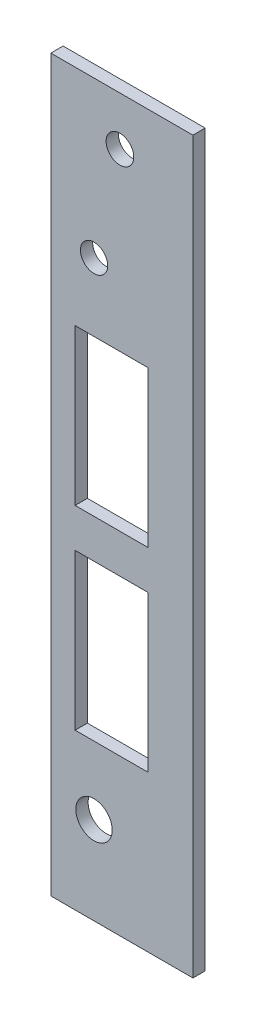
SolidWorks part; units mm, degrees
ref_plane "Front" through (0, 0, 0) normal (0, 0, 1) x (1, 0, 0)
ref_plane "Top" through (0, 0, 0) normal (0, 1, 0) x (1, 0, 0)
ref_plane "Right" through (0, 0, 0) normal (1, 0, 0) x (0, 0, -1)
sketch "Sketch1" plane through (0, 0, 0) normal (0, 0, 1) x (1, 0, 0)
  line L1 (0, 0) -> (18.542, 0)
  line L2 (0, 0) -> (0, -95.25)
  line L3 (0, -95.25) -> (18.542, -95.25)
  line L4 (18.542, 0) -> (18.542, -95.25)
  dimension "D1" = 18.542
  dimension "D2" = 95.25
extrude "Extrude1" add sketch "Sketch1" along normal blind 1.6002
sketch "Sketch2" plane through (0, 0, 1.6002) normal (0, 0, 1) x (1, 0, 0)
  line L0 (18.542, -95.25) -> (18.542, 0) construction
  line L1 (18.542, 0) -> (0, 0) construction
  circle A0 centre (9.017, -6.35) radius 1.8034
  dimension "D1" = 3.6068
  dimension "D3" = 9.525
  dimension "D4" = 6.35
extrude "Cut-Extrude1" cut sketch "Sketch2" against normal blind 1.6002
sketch "Sketch3" plane through (0, 0, 1.6002) normal (0, 0, 1) x (1, 0, 0)
  line L0 (0, -95.25) -> (18.542, -95.25) construction
  line L2 (0, 0) -> (0, -95.25) construction
  circle A0 centre (5.6388, -20.32) radius 1.778
  circle A1 centre (5.6388, -83.82) radius 2.3749
  dimension "D1" = 3.556
  dimension "D2" = 4.7498
  dimension "D3" = 11.43
  dimension "D4" = 5.6388
  dimension "D5" = 63.5
extrude "Cut-Extrude2" cut sketch "Sketch3" against normal blind 2.54
sketch "Sketch4" plane through (0, 0, 1.6002) normal (0, 0, 1) x (1, 0, 0)
  line L1 (3.175, -29.21) -> (12.7, -29.21)
  line L2 (3.175, -29.21) -> (3.175, -49.53)
  line L3 (3.175, -49.53) -> (12.7, -49.53)
  line L4 (12.7, -29.21) -> (12.7, -49.53)
  line L5 (3.175, -54.61) -> (12.7, -54.61)
  line L6 (3.175, -54.61) -> (3.175, -74.93)
  line L7 (3.175, -74.93) -> (12.7, -74.93)
  line L8 (12.7, -54.61) -> (12.7, -74.93)
  line L9 (0, 0) -> (0, -95.25) construction
  circle A1 centre (5.6388, -83.82) radius 2.3749 construction
  circle A2 centre (5.6388, -20.32) radius 1.778 construction
  dimension "D3" = 9.525
  dimension "D2" = 8.89
  dimension "D7" = 8.89
  dimension "D1" = 20.32
  dimension "D4" = 3.175
  dimension "D5" = 20.32
  dimension "D6" = 9.525
  dimension "D8" = 3.175
extrude "Fiber Holes" cut sketch "Sketch4" against normal blind 2.54
